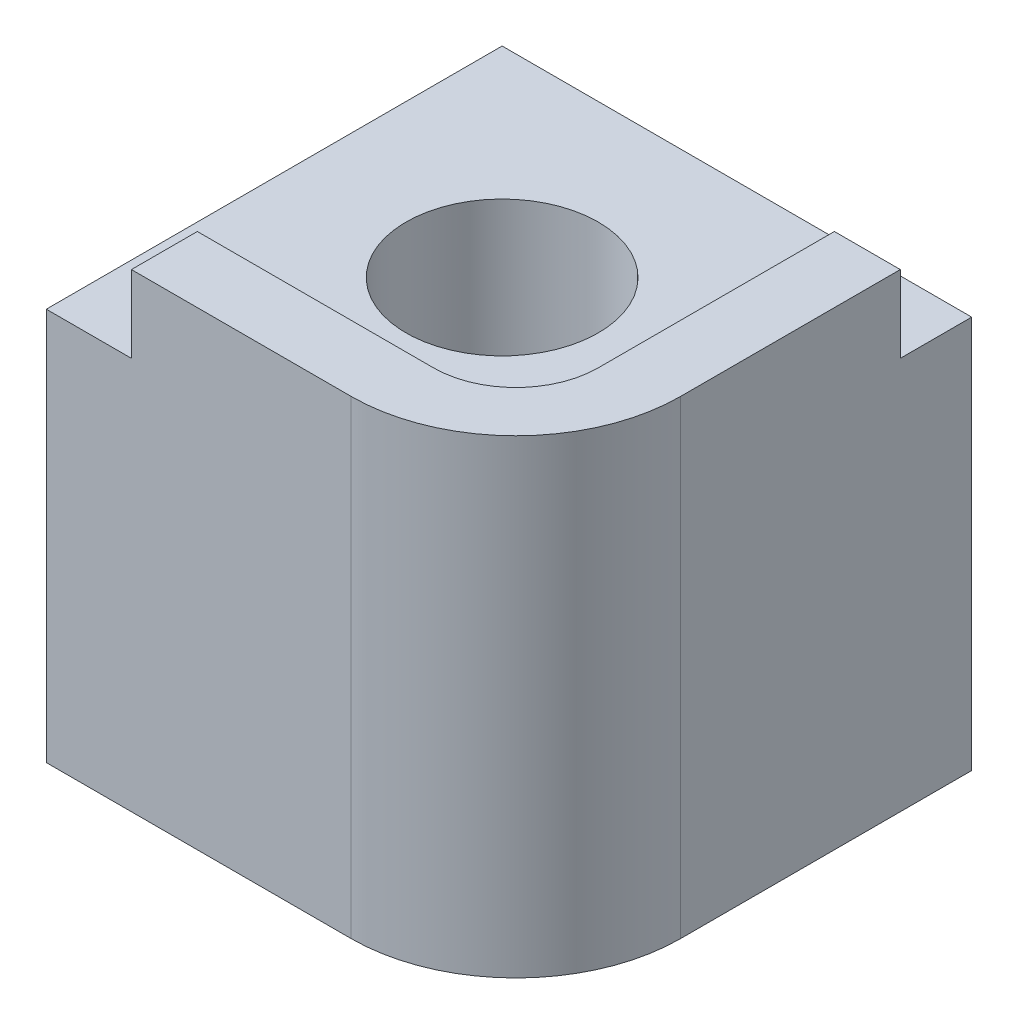
SolidWorks part; units mm, degrees
material "5052-H32"
ref_plane "Front Plane" through (0, 0, 0) normal (0, 0, 1) x (1, 0, 0)
ref_plane "Top Plane" through (0, 0, 0) normal (0, 1, 0) x (1, 0, 0)
ref_plane "Right Plane" through (0, 0, 0) normal (1, 0, 0) x (0, 0, -1)
sketch "Sketch1" plane through (0, 0, 0) normal (0, 0, 1) x (1, 0, 0)
  line L1 (0, 0) -> (8.55, 0)
  line L2 (0, 0) -> (0, 8.55)
  line L3 (0, 8.55) -> (8.55, 8.55)
  line L4 (8.55, 0) -> (8.55, 8.55)
  dimension "D1" = 8.55
  dimension "D2" = 8.55
extrude "Boss-Extrude1" add sketch "Sketch1" along normal blind 8.3
sketch "Sketch2" plane through (0, 0, 8.3) normal (0, 0, 1) x (1, 0, 0)
  line L0 (8.55, 0) -> (8.55, 8.55) construction
  line L1 (0, 8.55) -> (1.55, 8.55)
  line L2 (0, 8.55) -> (0, 7.15)
  line L3 (0, 7.15) -> (1.55, 7.15)
  line L4 (1.55, 8.55) -> (1.55, 7.15)
  dimension "D1" = 7
  dimension "D2" = 1.4
extrude "Cut-Extrude1" cut sketch "Sketch2" against normal through all
sketch "Sketch3" plane through (8.55, 0, 0) normal (1, 0, 0) x (0, 0, -1)
  line L0 (-8.3, 0) -> (-8.3, 8.55) construction
  line L1 (0, 8.55) -> (-1.3, 8.55)
  line L2 (0, 8.55) -> (0, 7.15)
  line L3 (0, 7.15) -> (-1.3, 7.15)
  line L4 (-1.3, 8.55) -> (-1.3, 7.15)
  dimension "D1" = 7
  dimension "D2" = 1.4
extrude "Cut-Extrude2" cut sketch "Sketch3" against normal through all
sketch "Sketch4" plane through (0, 8.55, 0) normal (0, 1, 0) x (1, 0, 0)
  line L0 (8.55, -8.3) -> (8.55, -1.3) construction
  line L1 (1.55, -1.3) -> (7.35, -1.3)
  line L2 (1.55, -1.3) -> (1.55, -7.1)
  line L3 (1.55, -7.1) -> (7.35, -7.1)
  line L4 (7.35, -1.3) -> (7.35, -7.1)
  line L5 (8.55, -8.3) -> (1.55, -8.3) construction
  dimension "D1" = 1.2
  dimension "D2" = 1.2
extrude "Cut-Extrude3" cut sketch "Sketch4" against normal blind 1.4
fillet "Fillet1" radius 1.5 1 edges at (7.35, 7.85, 7.1)
fillet "Fillet2" radius 3 1 edges at (8.55, 4.275, 8.3)
sketch "Sketch5" plane through (0, 0, 0) normal (0, -1, 0) x (1, 0, 0)
  line L0 (0, 0) -> (8.55, 0) construction
  line L1 (0, 8.3) -> (0, 0) construction
  circle A0 centre (3.65, 3.65) radius 1.75
  dimension "D1" = 3.65
  dimension "D2" = 3.65
extrude "Cut-Extrude4" cut sketch "Sketch5" against normal through all
chamfer "Chamfer1" distance 0.5 angle 35 1 edges at (3.65, 0, 1.9)
